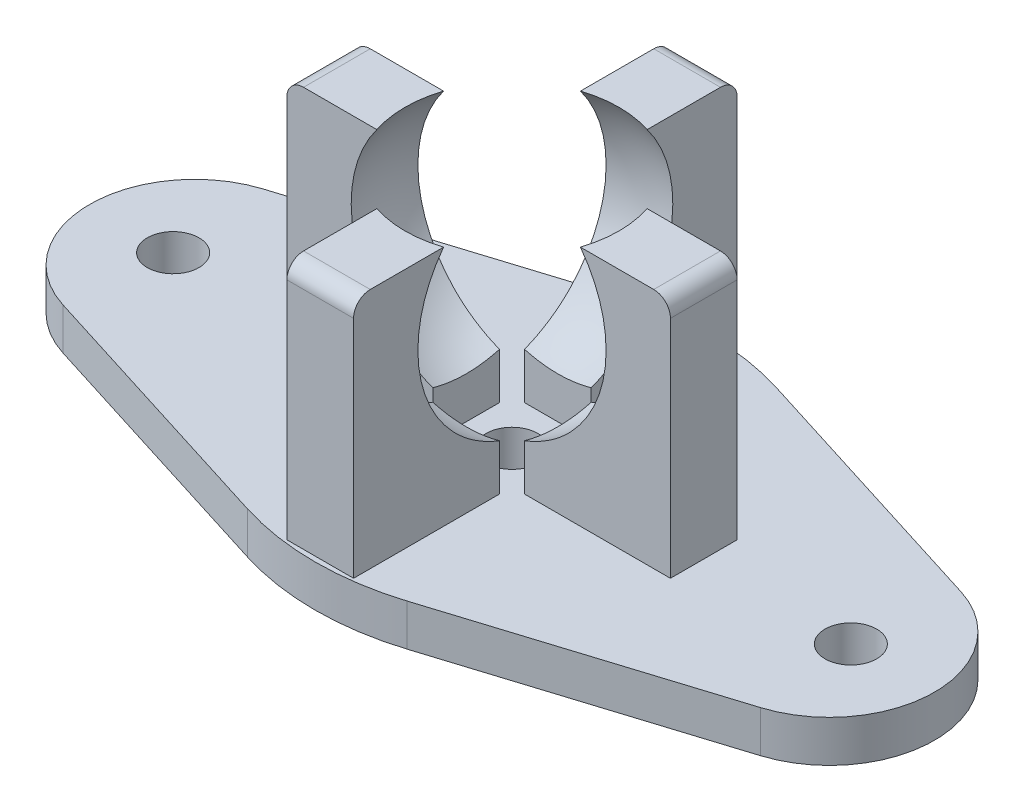
SolidWorks part; units mm, degrees
ref_plane "Front Plane" through (0, 0, 0) normal (0, 0, 1) x (1, 0, 0)
ref_plane "Top Plane" through (0, 0, 0) normal (0, 1, 0) x (1, 0, 0)
ref_plane "Right Plane" through (0, 0, 0) normal (1, 0, 0) x (0, 0, -1)
sketch "Sketch1" plane through (0, 0, 0) normal (0, 1, 0) x (1, 0, 0)
  line L0 (0, 12.5772) -> (-40.0726, 0)
  line L1 (-40.0726, 0) -> (0, -12.5772)
  line L2 (0, -12.5772) -> (40.0726, 0)
  line L3 (40.0726, 0) -> (0, 12.5772)
  line L4 (-40.0726, 0) -> (40.0726, 0) construction
  line L5 (0, 12.5772) -> (0, -12.5772) construction
  dimension "D1" = 24
  dimension "D2" = 42
extrude "Boss-Extrude1" add sketch "Sketch1" along normal blind 2.5
fillet "Fillet1" radius 16 2 edges at (0, 1.25, 12.5772) (0, 1.25, -12.5772)
fillet "Fillet2" radius 6.3 2 edges at (-40.0726, 1.25, 0) (40.0726, 1.25, 0)
sketch "Sketch2" plane through (0, 2.5, 0) normal (0, 1, 0) x (1, 0, 0)
  line L0 (2, 2) -> (11.5, 2)
  line L1 (-2, 2) -> (-2, 11.5)
  line L2 (2, -11.5) -> (2, -2)
  line L3 (-11.5, -2) -> (-2, -2)
  line L4 (-2, -11.5) -> (-2, -2)
  line L5 (-11.5, 2) -> (-2, 2)
  line L6 (2, 2) -> (2, 11.5)
  line L7 (2, -2) -> (11.5, -2)
  line L8 (-11.5, 2) -> (-11.5, -2)
  line L9 (-2, -11.5) -> (2, -11.5)
  line L10 (11.5, 2) -> (11.5, -2)
  line L11 (2, 11.5) -> (-2, 11.5)
  line L12 (0, 11.5) -> (0, -11.5) construction
  line L13 (-11.5, 0) -> (11.5, 0) construction
  dimension "D1" = 4
  dimension "D2" = 4
  dimension "D3" = 23
  dimension "D4" = 23
  dimension "D5" = 9.5
  dimension "D6" = 9.5
extrude "Boss-Extrude2" add sketch "Sketch2" along normal blind 14.5
sketch "Sketch3" plane through (0, 0, 0) normal (0, 0, 1) x (1, 0, 0)
  line L0 (0, 20.3) -> (0, 4.5)
  line L1 (4.7913, 2.5) -> (-4.7913, 2.5) construction
  arc A0 (0, 4.5) -> (0, 20.3) centre (0, 12.4) ccw
  dimension "D1" = 15.8
  dimension "D2" = 2
revolve "Cut-Revolve1" cut sketch "Sketch3" angle 360 about L0
fillet "Fillet3" radius 1 4 edges at (0, 17, -11.5) (-11.5, 17, 0) (0, 17, 11.5) (11.5, 17, 0)
sketch "Sketch5" plane through (0, 2.5, 0) normal (0, 1, 0) x (1, 0, 0)
  line L1 (-2.75, 2.75) -> (2.75, 2.75)
  line L2 (-2.75, 2.75) -> (-2.75, -2.75)
  line L3 (-2.75, -2.75) -> (2.75, -2.75)
  line L4 (2.75, 2.75) -> (2.75, -2.75)
  line L5 (-2.75, 2.75) -> (2.75, -2.75) construction
  line L6 (-2.75, -2.75) -> (2.75, 2.75) construction
  point P0 (0, 0)
  dimension "D1" = 5.5
  dimension "D2" = 5.5
extrude "Cut-Extrude1" cut sketch "Sketch5" along normal offset from surface (31.9598 mm away) 14.5
sketch "Sketch6" plane through (0, 2.5, 0) normal (0, 1, 0) x (1, 0, 0)
  circle A0 centre (0, 0) radius 1.55
  dimension "D1" = 3.1
extrude "Cut-Extrude2" cut sketch "Sketch6" against normal up to surface (2.5 mm away) up to face at (0, 0, 0)
sketch "Sketch7" plane through (0, 2.5, 0) normal (0, 1, 0) x (1, 0, 0)
  line L0 (0, 0) -> (0, -11.5) construction
  line L1 (-2, -11.5) -> (2, -11.5) construction
  circle A0 centre (20.32, 0) radius 1.55
  circle A1 centre (-20.32, 0) radius 1.55
  dimension "D2" = 3.1
  dimension "D1" = 40.64
extrude "Cut-Extrude3" cut sketch "Sketch7" against normal up to surface (2.5 mm away) up to face at (0, 0, 1.55)
